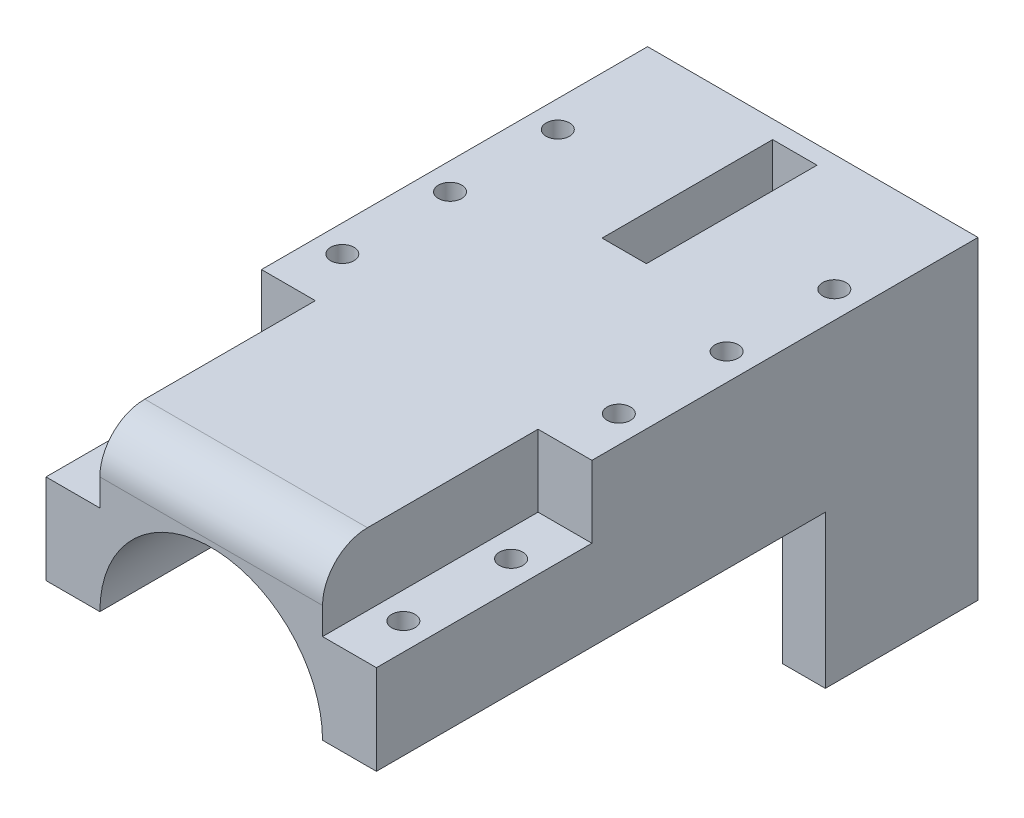
SolidWorks part; units mm, degrees
ref_plane "Plan de face" through (0, 0, 0) normal (0, 0, 1) x (1, 0, 0)
ref_plane "Plan de dessus" through (0, 0, 0) normal (0, 1, 0) x (1, 0, 0)
ref_plane "Plan de droite" through (0, 0, 0) normal (1, 0, 0) x (0, 0, -1)
sketch "Esquisse1" plane through (0, 0, 0) normal (0, 0, 1) x (1, 0, 0)
  line L0 (0, 0) -> (-84.6745, 0) construction
  line L1 (0, 0) -> (94.0931, 0) construction
  line L2 (-12.4, 0) -> (-18.4, 0)
  line L3 (0, 0) -> (0, 12.4) construction
  line L4 (-18.4, 0) -> (-18.4, 18)
  line L5 (-18.4, 18) -> (18.4, 18)
  line L6 (18.4, 0) -> (18.4, 18)
  line L7 (12.4, 0) -> (18.4, 0)
  line L8 (0, 12.4) -> (0, 18) construction
  arc A0 (-12.4, 0) -> (12.4, 0) centre (0, 0) cw
  point P11 (0, 18)
  dimension "D1" = 6
  dimension "D2" = 18
extrude "Boss.-Extru.1" add sketch "Esquisse1" along normal blind 132
sketch "Esquisse3" plane through (0, 18, 0) normal (0, -1, 0) x (1, 0, 0)
  line L0 (-18.4, 66) -> (18.4, 66) construction
  line L3 (0, 66) -> (0, 73.4675) construction
  line L4 (-18.4, 132) -> (-18.4, 0) construction
  line L5 (2.4701, 46) -> (-2.4701, 46)
  line L6 (2.4701, 46) -> (2.4701, 86)
  line L7 (2.4701, 86) -> (-2.4701, 86)
  line L8 (-2.4701, 46) -> (-2.4701, 86)
  line L9 (2.4701, 46) -> (-2.4701, 86) construction
  line L10 (2.4701, 86) -> (-2.4701, 46) construction
  dimension "D1" = 40
extrude "Enlèv. mat.-Extru.2" cut sketch "Esquisse3" along normal blind 9
sketch "Esquisse4" plane through (0, 18, 0) normal (0, 1, 0) x (1, 0, 0)
  line L0 (18.4, -12) -> (-19.7679, -12) construction
  line L1 (0, 0) -> (0, -28.5028) construction
  line L2 (15.4, 0) -> (15.4, -28.5028) construction
  line L3 (18.4, -6) -> (-18.4211, -6) construction
  line L4 (18.4, 0) -> (-18.4, 0) construction
  line L5 (18.4, -132) -> (18.4, 0) construction
  line L6 (18.4, -66) -> (-18.4, -66) construction
  line L7 (-18.4, -132) -> (-18.4, 0) construction
  circle A0 centre (15.4, -6) radius 1.3
  circle A1 centre (15.4, -18) radius 1.3
  circle A2 centre (-15.4, -6) radius 1.3
  circle A3 centre (-15.4, -18) radius 1.3
  circle A4 centre (15.4, -30) radius 1.3
  circle A5 centre (-15.4, -30) radius 1.3
  circle A6 centre (15.4, -42) radius 1.3
  circle A7 centre (-15.4, -42) radius 1.3
  circle A10 centre (-15.4, -126) radius 1.3
  circle A11 centre (-15.4, -114) radius 1.3
  circle A12 centre (-15.4, -102) radius 1.3
  circle A13 centre (-15.4, -90) radius 1.3
  circle A14 centre (-15.4, -78) radius 1.3
  circle A15 centre (15.4, -78) radius 1.3
  circle A16 centre (15.4, -90) radius 1.3
  circle A17 centre (15.4, -102) radius 1.3
  circle A18 centre (15.4, -114) radius 1.3
  circle A19 centre (15.4, -126) radius 1.3
  circle A20 centre (15.4, -54) radius 1.3 [skipped]
  circle A21 centre (-15.4, -54) radius 1.3 [skipped]
  dimension "D1" = 3
  dimension "D2" = 6
  dimension "D3" = 6
  dimension "D4" = 5
extrude "Enlèv. mat.-Extru.3" cut sketch "Esquisse4" against normal blind 18
sketch "Esquisse5" plane through (0, 18, 0) normal (0, 1, 0) x (1, 0, 0)
  line L0 (0, 0) -> (0, -132) construction
  line L1 (18.4, 0) -> (12.4, 0)
  line L2 (18.4, 0) -> (18.4, -24)
  line L3 (18.4, -24) -> (12.4, -24)
  line L4 (12.4, 0) -> (12.4, -24)
  line L5 (18.4, 0) -> (-18.4, 0) construction
  line L6 (18.4, -132) -> (-18.4, -132) construction
  line L7 (18.4, -66) -> (-18.4, -66) construction
  line L8 (18.4, -132) -> (18.4, 0) construction
  line L9 (-18.4, -132) -> (-18.4, 0) construction
  line L10 (-18.4, -132) -> (-12.4, -132)
  line L11 (-12.4, -132) -> (-12.4, -108)
  line L12 (-18.4, -108) -> (-12.4, -108)
  line L13 (-18.4, -132) -> (-18.4, -108)
  line L14 (-18.4, 0) -> (-18.4, -24)
  line L15 (-18.4, -24) -> (-12.4, -24)
  line L16 (-12.4, 0) -> (-12.4, -24)
  line L17 (-18.4, 0) -> (-12.4, 0)
  line L18 (12.4, -132) -> (12.4, -108)
  line L19 (18.4, -108) -> (12.4, -108)
  line L20 (18.4, -132) -> (18.4, -108)
  line L21 (18.4, -132) -> (12.4, -132)
  dimension "D1" = 24
  dimension "D2" = 6
extrude "Enlèv. mat.-Extru.4" cut sketch "Esquisse5" against normal blind 8
sketch "Esquisse7" plane through (-18.4, 0, 0) normal (-1, 0, 0) x (0, 0, 1)
  line L0 (66, 18) -> (66, 0) construction
  line L1 (108, 18) -> (24, 18) construction
  line L2 (132, 0) -> (0, 0) construction
  line L4 (65, 0) -> (67, 0)
  line L5 (65, 0) -> (65, 18)
  line L6 (65, 18) -> (67, 18)
  line L7 (67, 0) -> (67, 18)
  line L8 (65, 0) -> (67, 18) construction
  line L9 (65, 18) -> (67, 0) construction
  point P6 (66, 9)
  dimension "D1" = 2
extrude "Boss.-Extru.2" add sketch "Esquisse7" against normal through all
sketch "Esquisse8" plane through (0, 0, 65) normal (0, 0, -1) x (-1, 0, 0)
  line L0 (0, 0) -> (16.5032, 0) construction
  line L1 (-12.4, 0) -> (12.4, 0) construction
  line L2 (0, 0) -> (-16.5316, 0) construction
  line L3 (12.775, 0) -> (-12.775, 0)
  arc A0 (12.775, 0) -> (-12.775, 0) centre (0, 0) ccw
extrude "Enlèv. mat.-Extru.5" cut sketch "Esquisse8" along normal blind 15
sketch "Esquisse9" plane through (0, 0, 67) normal (0, 0, 1) x (1, 0, 0)
  line L0 (0, 0) -> (13.8492, 0) construction
  line L1 (12.4, 0) -> (-12.4, 0) construction
  line L2 (0, 0) -> (-14.6616, 0) construction
  line L3 (12.775, 0) -> (-12.775, 0)
  arc A0 (12.775, 0) -> (-12.775, 0) centre (0, 0) ccw
extrude "Enlèv. mat.-Extru.6" cut sketch "Esquisse9" along normal blind 15
sketch "Esquisse10" plane through (0, 0, 0) normal (0, -1, 0) x (1, 0, 0)
  line L0 (12.775, 82) -> (18.4, 82)
  line L1 (18.4, 132) -> (18.4, 0) construction
  line L2 (12.775, 50) -> (18.4, 50)
  line L3 (18.4, 50) -> (18.4, 82)
  line L4 (12.775, 82) -> (12.775, 50)
  line L5 (0, 67) -> (0, 64.9415) construction
  line L6 (12.775, 67) -> (-12.775, 67) construction
  line L7 (-12.775, 50) -> (-18.4, 50)
  line L8 (-18.4, 50) -> (-18.4, 82)
  line L9 (-12.775, 82) -> (-12.775, 50)
  line L10 (-12.775, 82) -> (-18.4, 82)
extrude "Boss.-Extru.3" add sketch "Esquisse10" along normal blind 17
sketch "Esquisse14" plane through (18.4, 0, 0) normal (1, 0, 0) x (0, 0, -1)
  line L0 (-108, 18) -> (-24, 18) construction
  line L1 (-56.4694, 18) -> (-45.1194, 18)
  line L2 (-56.4694, 18) -> (-56.4694, 10.412)
  line L3 (-56.4694, 10.412) -> (-45.1194, 10.412)
  line L4 (-45.1194, 18) -> (-45.1194, 10.412)
extrude "Boss.-Extru.5" add sketch "Esquisse14" along normal blind 6
sketch "Esquisse16" plane through (24.4, 0, 0) normal (1, 0, 0) x (0, 0, -1)
  line L1 (-43.9372, 13.05) -> (-57.196, 13.05)
  line L2 (-43.9372, 13.05) -> (-43.9372, 8.7778)
  line L3 (-43.9372, 8.7778) -> (-57.196, 8.7778)
  line L4 (-57.196, 13.05) -> (-57.196, 8.7778)
extrude "Enlèv. mat.-Extru.7" cut sketch "Esquisse16" against normal blind 11
sketch "Esquisse17" plane through (18.4, 0, 0) normal (1, 0, 0) x (0, 0, -1)
  line L0 (-45.1194, 18) -> (-24, 18) construction
  line L1 (-29.1148, 18) -> (-13.5015, 18)
  line L2 (-29.1148, 18) -> (-29.1148, 12.8991)
  line L3 (-29.1148, 12.8991) -> (-13.5015, 12.8991)
  line L4 (-13.5015, 18) -> (-13.5015, 12.8991)
extrude "Boss.-Extru.6" add sketch "Esquisse17" along normal blind 11 and the other way blind 11
sketch "Esquisse11" plane through (0, 18, 0) normal (0, 1, 0) x (1, 0, 0)
  line L0 (-18.4, -66) -> (18.5601, -66) construction
  line L1 (-18.4, -108) -> (-18.4, -24) construction
  line L2 (15.4, -6) -> (15.4, -18) construction
  line L3 (-35.4042, -116) -> (36.1198, -116) construction
  line L4 (-37.228, -16) -> (37.9436, -16) construction
  line L5 (0, -132) -> (0, 0) construction
  line L6 (26.63, -116) -> (26.63, -16) construction
  line L7 (-26.63, -116) -> (-26.63, -16) construction
  line L8 (12.4, -132) -> (-12.4, -132) construction
  line L9 (12.4, 0) -> (-12.4, 0) construction
  line L10 (24.22, -116) -> (24.22, -16) construction
  line L11 (26.63, -102) -> (-26.63, -102) construction
  line L12 (19.13, -116) -> (19.13, -16) construction
  line L13 (-26.63, -51) -> (26.63, -51) construction
  line L14 (26.63, -20.6) -> (-26.63, -20.6) construction
  line L15 (-8.37, -116) -> (-8.37, -16) construction
  line L16 (-23.98, -116) -> (-23.98, -16) construction
  line L17 (26.63, -101) -> (-26.63, -101) construction
  line L18 (-26.63, -28) -> (26.63, -28) construction
  circle A0 centre (24.22, -102) radius 1.85
  circle A1 centre (19.13, -51) radius 1.85
  circle A2 centre (24.22, -20.6) radius 1.85
  circle A3 centre (-8.37, -51) radius 1.85
  circle A4 centre (15.4, -6) radius 1.3
  circle A5 centre (15.4, -18) radius 2.9164
  circle A6 centre (-23.98, -101) radius 1.85
  circle A7 centre (-23.98, -28) radius 1.85
  dimension "D8" = 65
  dimension "D9" = 4.6
  dimension "D10" = 35
  dimension "D11" = 2.65
  dimension "D13" = 12
  dimension "D1" = 50
  dimension "D2" = 50
  dimension "D3" = 26.63
  dimension "D4" = 26.63
  dimension "D5" = 2.41
  dimension "D6" = 14
  dimension "D7" = 7.5
  dimension "D12" = 15
extrude "Enlèv. mat.-Extru.8" cut sketch "Esquisse11" against normal blind 8
sketch "Esquisse18" plane through (-2.4701, 0, 0) normal (1, 0, 0) x (0, 0, -1)
  line L1 (-55.739, 13.14) -> (-46.0613, 13.14)
  line L2 (-55.739, 13.14) -> (-55.739, 4.8868)
  line L3 (-55.739, 4.8868) -> (-46.0613, 4.8868)
  line L4 (-46.0613, 13.14) -> (-46.0613, 4.8868)
extrude "Enlèv. mat.-Extru.9" cut sketch "Esquisse18" against normal blind 10
fillet "Congé2" radius 5 2 edges at (0, 18, 0) (0, 18, 132)
sketch "Esquisse20" plane through (0, 0, 0) normal (0, -1, 0) x (1, 0, 0)
  line L0 (0, 67) -> (0, 65) construction
  line L1 (12.775, 67) -> (-12.775, 67) construction
  line L2 (12.775, 65) -> (-12.775, 65) construction
  line L4 (-13.65, 45.9837) -> (13.65, 45.9837)
  line L5 (-13.65, 45.9837) -> (-13.65, 86.0163)
  line L6 (-13.65, 86.0163) -> (13.65, 86.0163)
  line L7 (13.65, 45.9837) -> (13.65, 86.0163)
  line L8 (-13.65, 45.9837) -> (13.65, 86.0163) construction
  line L9 (-13.65, 86.0163) -> (13.65, 45.9837) construction
  point P6 (0, 66)
  dimension "D1" = 27.3
extrude "Enlèv. mat.-Extru.11" cut sketch "Esquisse20" along normal blind 22
sketch "Esquisse22" plane through (0, 13.05, 0) normal (0, -1, 0) x (1, 0, 0)
  circle A0 centre (19.13, 51) radius 2.7804
extrude "Enlèv. mat.-Extru.12" cut sketch "Esquisse22" along normal blind 33
sketch "Esquisse23" plane through (0, 13.14, 0) normal (0, -1, 0) x (1, 0, 0)
  line L0 (-10.9627, 54.7361) -> (-30.5745, 60.2092)
  line L1 (-30.5745, 60.2092) -> (-30.5745, 54.652)
  line L2 (-30.5745, 54.652) -> (-10.9627, 50.3961)
  line L3 (-10.9627, 50.3961) -> (-10.9627, 54.7361)
extrude "Enlèv. mat.-Extru.13" cut sketch "Esquisse23" along normal blind 23
sketch "Esquisse24" plane through (0, 0, 65) normal (0, 0, -1) x (-1, 0, 0)
  line L1 (45.9642, -26.5503) -> (-55.6045, -26.5503)
  line L2 (45.9642, -26.5503) -> (45.9642, 38.3462)
  line L3 (45.9642, 38.3462) -> (-55.6045, 38.3462)
  line L4 (-55.6045, -26.5503) -> (-55.6045, 38.3462)
extrude "Enlèv. mat.-Extru.14" cut sketch "Esquisse24" along normal blind 80
